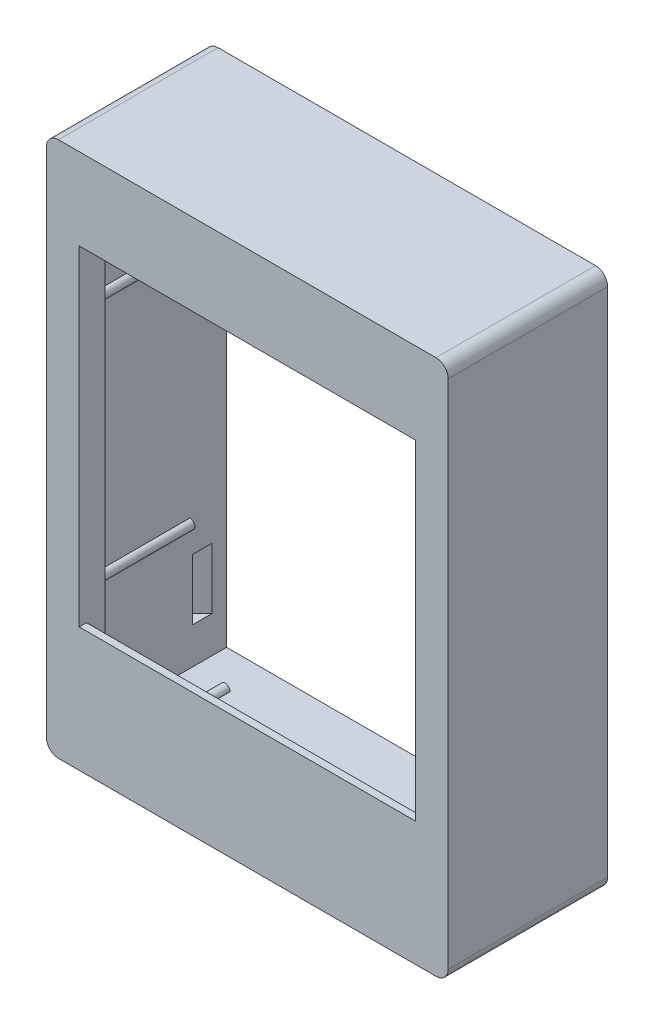
SolidWorks part; units mm, degrees
ref_plane "前视基准面" through (0, 0, 0) normal (0, 0, 1) x (1, 0, 0)
ref_plane "上视基准面" through (0, 0, 0) normal (0, 1, 0) x (1, 0, 0)
ref_plane "右视基准面" through (0, 0, 0) normal (1, 0, 0) x (0, 0, -1)
sketch "草图1" plane through (0, 0, 0) normal (0, 0, 1) x (1, 0, 0)
  line L1 (0, 0) -> (33, 0)
  line L2 (0, 0) -> (0, 44)
  line L3 (0, 44) -> (33, 44)
  line L4 (33, 0) -> (33, 44)
  dimension "D1" = 33
  dimension "D2" = 44
extrude "凸台-拉伸1" add sketch "草图1" along normal blind 12.5
sketch "草图2" plane through (0, 0, 0) normal (0, 0, -1) x (-1, 0, 0)
  line L12 (-31.3, 1.7) -> (-1.7, 1.7)
  line L13 (-1.7, 1.7) -> (-1.7, 42.3)
  line L14 (-1.7, 42.3) -> (-31.3, 42.3)
  line L15 (-31.3, 42.3) -> (-31.3, 1.7)
  line L16 (-31.3, 1.7) -> (-1.7, 1.7)
  line L17 (-1.7, 1.7) -> (-1.7, 42.3)
  line L18 (-1.7, 42.3) -> (-31.3, 42.3)
  line L19 (-31.3, 42.3) -> (-31.3, 1.7)
  dimension "D1" = 1.7
extrude "切除-拉伸2" cut sketch "草图2" against normal blind 11
sketch "草图3" plane through (0, 0, 11) normal (0, 0, -1) x (-1, 0, 0)
  line L0 (-31.3, 42.3) -> (-31.3, 1.7) construction
  line L1 (-30.3, 37.3) -> (-2.7, 37.3)
  line L2 (-30.3, 37.3) -> (-30.3, 6.2)
  line L3 (-30.3, 6.2) -> (-2.7, 6.2)
  line L4 (-2.7, 37.3) -> (-2.7, 6.2)
  line L5 (-1.7, 1.7) -> (-1.7, 42.3) construction
  line L6 (-1.7, 42.3) -> (-31.3, 42.3) construction
  line L7 (-31.3, 1.7) -> (-1.7, 1.7) construction
  dimension "D1" = 1
  dimension "D2" = 1
  dimension "D3" = 5
  dimension "D4" = 4.5
  dimension "D5" = 31.1
  dimension "D6" = 27.6
extrude "切除-拉伸3" cut sketch "草图3" against normal through all
sketch "草图4" plane through (0, 0, 11) normal (0, 0, -1) x (-1, 0, 0)
  line L0 (-16.5, 42.3) -> (-16.5, 1.7) construction
  line L1 (-1.7, 42.3) -> (-31.3, 42.3) construction
  line L2 (-31.3, 1.7) -> (-1.7, 1.7) construction
  line L3 (-2.7, 37.3) -> (-30.3, 37.3) construction
  line L4 (-25.5, 42.3) -> (-7.5, 42.3)
  line L5 (-25.5, 42.3) -> (-25.5, 39.3)
  line L6 (-25.5, 39.3) -> (-7.5, 39.3)
  line L7 (-7.5, 42.3) -> (-7.5, 39.3)
  point P10 (-16.5, 42.3)
  dimension "D1" = 18
  dimension "D2" = 3
  dimension "D3" = 2
extrude "切除-拉伸4" cut sketch "草图4" against normal blind 0.7
fillet "圆角1" radius 1 4 edges at (0, 0, 6.25) (0, 44, 6.25) (33, 44, 6.25) (33, 0, 6.25)
sketch "草图5" plane through (0, 6.2, 0) normal (0, 1, 0) x (1, 0, 0)
  line L1 (2.7, -12.5) -> (30.3, -12.5)
  line L2 (2.7, -12.5) -> (2.7, -11.9)
  line L3 (2.7, -11.9) -> (30.3, -11.9)
  line L4 (30.3, -12.5) -> (30.3, -11.9)
  dimension "D1" = 0.6
extrude "凸台-拉伸2" add sketch "草图5" along normal blind 1
sketch "草图6" plane through (0, 0, 11) normal (0, 0, -1) x (-1, 0, 0)
  line L0 (-31.3, 22) -> (-1.7, 22) construction
  line L1 (-31.3, 42.3) -> (-31.3, 1.7) construction
  line L2 (-1.7, 1.7) -> (-1.7, 42.3) construction
  line L3 (-31.3, 11.6) -> (-31.3, 12.4)
  line L4 (-16.5, 42.3) -> (-16.5, 1.7) construction
  line L5 (-1.7, 42.3) -> (-31.3, 42.3) construction
  line L6 (-31.3, 1.7) -> (-1.7, 1.7) construction
  line L7 (-25.5, 42.3) -> (-31.3, 42.3) construction
  line L8 (-31.3, 42.3) -> (-31.3, 1.7) construction
  line L9 (-31.3, 32.4) -> (-31.3, 31.6)
  line L10 (-28.8, 42.3) -> (-28, 42.3)
  line L11 (-28.8, 1.7) -> (-28, 1.7)
  line L12 (-4.2, 1.7) -> (-5, 1.7)
  line L13 (-4.2, 42.3) -> (-5, 42.3)
  line L14 (-1.7, 32.4) -> (-1.7, 31.6)
  line L15 (-1.7, 11.6) -> (-1.7, 12.4)
  arc A0 (-28.8, 42.3) -> (-28, 42.3) centre (-28.4, 42.3) ccw
  arc A1 (-31.3, 31.6) -> (-31.3, 32.4) centre (-31.3, 32) ccw
  arc A2 (-31.3, 12.4) -> (-31.3, 11.6) centre (-31.3, 12) cw
  arc A3 (-28.8, 1.7) -> (-28, 1.7) centre (-28.4, 1.7) cw
  arc A4 (-4.2, 1.7) -> (-5, 1.7) centre (-4.6, 1.7) ccw
  arc A5 (-1.7, 12.4) -> (-1.7, 11.6) centre (-1.7, 12) ccw
  arc A6 (-1.7, 31.6) -> (-1.7, 32.4) centre (-1.7, 32) cw
  arc A7 (-4.2, 42.3) -> (-5, 42.3) centre (-4.6, 42.3) cw
  dimension "D1" = 0.4
  dimension "D2" = 0.4
  dimension "D3" = 10
extrude "凸台-拉伸3" add sketch "草图6" along normal blind 8
sketch "草图7" plane through (0, 0, 12.5) normal (0, 0, 1) x (1, 0, 0)
  line L4 (0, 43) -> (0, 1)
  line L5 (1, 0) -> (32, 0)
  line L6 (33, 1) -> (33, 43)
  line L7 (32, 44) -> (1, 44)
  line L8 (0, 43) -> (0, 1)
  line L9 (1, 0) -> (32, 0)
  line L10 (33, 1) -> (33, 43)
  line L11 (32, 44) -> (1, 44)
  arc A4 (0, 1) -> (1, 0) centre (1, 1) ccw
  arc A5 (32, 0) -> (33, 1) centre (32, 1) ccw
  arc A6 (33, 43) -> (32, 44) centre (32, 43) ccw
  arc A7 (1, 44) -> (0, 43) centre (1, 43) ccw
  arc A8 (0, 1) -> (1, 0) centre (1, 1) ccw
  arc A9 (32, 0) -> (33, 1) centre (32, 1) ccw
  arc A10 (33, 43) -> (32, 44) centre (32, 43) ccw
  arc A11 (1, 44) -> (0, 43) centre (1, 43) ccw
  dimension "D1" = 0
extrude "凸台-拉伸4" add sketch "草图7" along normal blind 0.6
sketch "草图8" plane through (0, 0, 12.5) normal (0, 0, -1) x (-1, 0, 0)
  line L0 (-2.7, 6.2) -> (-2.7, 37.3) construction
  line L1 (-30.3, 37.3) -> (-2.7, 37.3)
  line L2 (-30.3, 37.3) -> (-30.3, 10.2)
  line L3 (-30.3, 10.2) -> (-2.7, 10.2)
  line L4 (-2.7, 37.3) -> (-2.7, 10.2)
  line L5 (-30.3, 7.2) -> (-2.7, 7.2) construction
  dimension "D1" = 3
extrude "切除-拉伸5" cut sketch "草图8" against normal through all
ref_plane "基准面1" through (0, 34.3, 0) normal (0, -1, 0) x (-1, 0, 0)
sketch "草图9" plane through (0, 34.3, 0) normal (0, -1, 0) x (-1, 0, 0)
  line L0 (-31.3, -1.2) -> (-32.1, -2)
  line L1 (-32.1, -2) -> (-31.3, -2.8)
  line L2 (-31.3, -2.8) -> (-31.3, -1.2)
  line L3 (-32.1, -2) -> (-1.7, -2) construction
  line L4 (-16.5, 0) -> (-16.5, -11.7) construction
  line L5 (-1.7, -2.8) -> (-1.7, -1.2)
  line L6 (-1.7, -1.2) -> (-0.9, -2)
  line L7 (-0.9, -2) -> (-1.7, -2.8)
  line L16 (-4.2, -3) -> (-4.2, -11)
  line L17 (-4.2, -11) -> (-1.7, -11)
  line L18 (-1.7, -11) -> (-1.7, 0)
  line L19 (-1.7, 0) -> (-31.3, 0)
  line L20 (-31.3, 0) -> (-31.3, -11)
  line L21 (-31.3, -11) -> (-28.8, -11)
  line L22 (-28.8, -11) -> (-28.8, -3)
  line L23 (-28.8, -3) -> (-28, -3)
  line L24 (-28, -3) -> (-28, -11)
  line L25 (-28, -11) -> (-25.5, -11)
  line L26 (-25.5, -11) -> (-25.5, -11.7)
  line L27 (-25.5, -11.7) -> (-7.5, -11.7)
  line L28 (-7.5, -11.7) -> (-7.5, -11)
  line L29 (-7.5, -11) -> (-5, -11)
  line L30 (-5, -11) -> (-5, -3)
  line L31 (-5, -3) -> (-4.2, -3)
  line L32 (-4.2, -3) -> (-4.2, -11) construction
  line L33 (-4.2, -11) -> (-1.7, -11) construction
  line L34 (-1.7, -11) -> (-1.7, 0) construction
  line L35 (-1.7, 0) -> (-31.3, 0) construction
  line L36 (-31.3, 0) -> (-31.3, -11) construction
  line L37 (-31.3, -11) -> (-28.8, -11) construction
  line L38 (-28.8, -11) -> (-28.8, -3) construction
  line L39 (-28.8, -3) -> (-28, -3) construction
  line L40 (-28, -3) -> (-28, -11) construction
  line L41 (-28, -11) -> (-25.5, -11) construction
  line L42 (-25.5, -11) -> (-25.5, -11.7) construction
  line L43 (-25.5, -11.7) -> (-7.5, -11.7) construction
  line L44 (-7.5, -11.7) -> (-7.5, -11) construction
  line L45 (-7.5, -11) -> (-5, -11) construction
  line L46 (-5, -11) -> (-5, -3) construction
  line L47 (-5, -3) -> (-4.2, -3) construction
  dimension "D2" = 0.8
  dimension "D3" = 2
  dimension "D1" = 0
extrude "切除-拉伸6" cut sketch "草图9" against normal blind 5
ref_plane "基准面2" through (0, 22, 0) normal (0, -1, 0) x (-1, 0, 0)
mirror "镜向1" about plane through (0, 22, 0) normal (0, -1, 0) of "切除-拉伸6"
